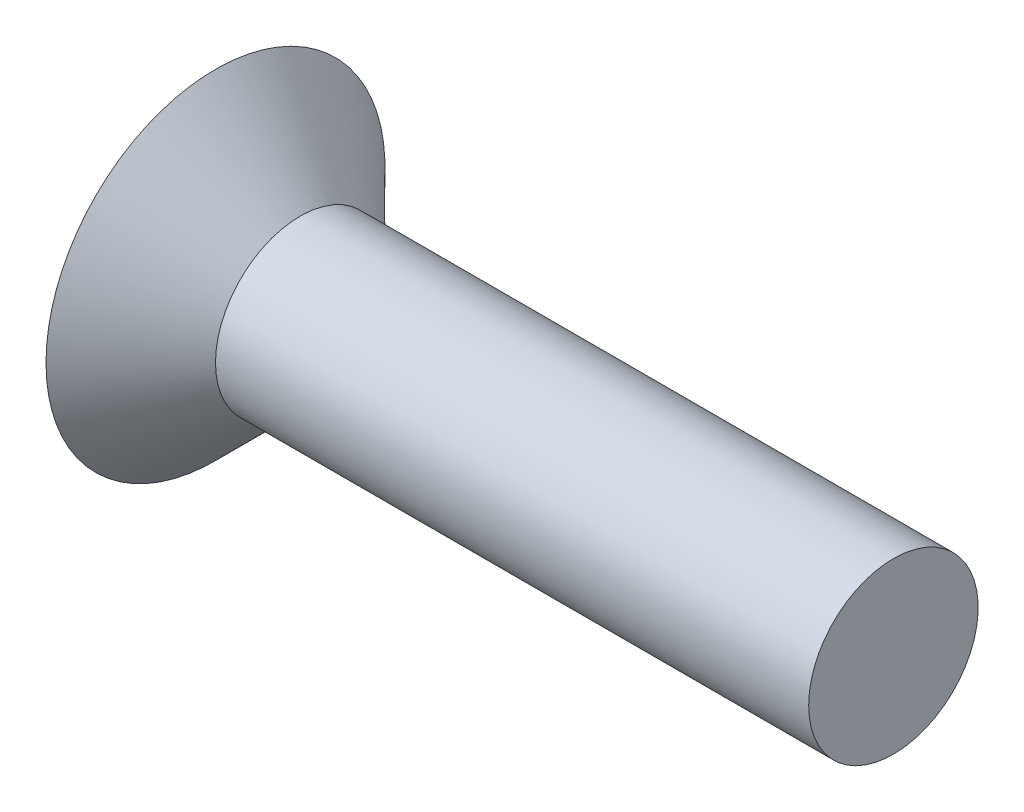
SolidWorks part; units mm, degrees
material "普通碳钢"
ref_plane "前视基准面" through (0, 0, 0) normal (0, 0, 1) x (1, 0, 0)
ref_plane "上视基准面" through (0, 0, 0) normal (0, 1, 0) x (1, 0, 0)
ref_plane "右视基准面" through (0, 0, 0) normal (1, 0, 0) x (0, 0, -1)
sketch "草图1" plane through (0, 0, 0) normal (0, 0, 1) x (1, 0, 0)
  line L0 (0, 0) -> (0, 3)
  line L5 (0, 0) -> (12, 0) construction
  line L6 (12, 0) -> (12, 1.5)
  line L7 (12, 1.5) -> (1.5, 1.5)
  line L8 (1.5, 1.5) -> (0, 3)
  dimension "D1" = 3
  dimension "D2" = 12
  dimension "D3" = 6
  dimension "D5" = 45
revolve "旋转1" add sketch "草图1" angle 360 about L5
cosmetic thread "装饰螺纹线2" parameters "D2"=1.221
sketch "草图2" plane through (0, 0, 0) normal (-1, 0, 0) x (0, 0, 1)
  line L1 (0, 1.1547) -> (-1, 0.5774)
  line L2 (-1, 0.5774) -> (-1, -0.5774)
  line L3 (-1, -0.5774) -> (0, -1.1547)
  line L4 (0, -1.1547) -> (1, -0.5774)
  line L5 (1, -0.5774) -> (1, 0.5774)
  line L6 (1, 0.5774) -> (0, 1.1547)
  circle A0 centre (0, 0) radius 1 construction
  dimension "D1" = 1
extrude "切除-拉伸1" cut sketch "草图2" against normal blind 1
